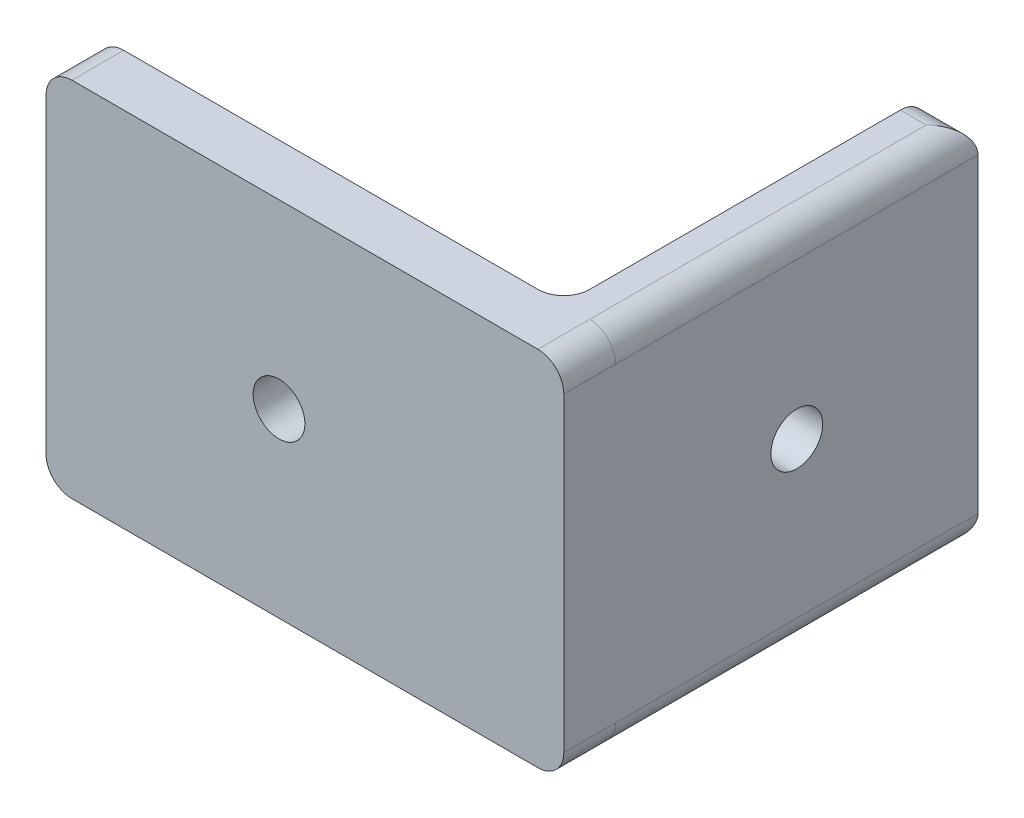
SolidWorks part; units mm, degrees
ref_plane "Front Plane" through (0, 0, 0) normal (0, 0, 1) x (1, 0, 0)
ref_plane "Top Plane" through (0, 0, 0) normal (0, 1, 0) x (1, 0, 0)
ref_plane "Right Plane" through (0, 0, 0) normal (1, 0, 0) x (0, 0, -1)
sketch "Sketch1" plane through (0, 0, 0) normal (0, 0, 1) x (1, 0, 0)
  line L1 (10, 0) -> (190, 0)
  line L2 (0, 10) -> (0, 130)
  line L3 (10, 140) -> (190, 140)
  line L4 (200, 10) -> (200, 130)
  arc A0 (190, 0) -> (200, 10) centre (190, 10) ccw
  arc A1 (190, 140) -> (200, 130) centre (190, 130) cw
  arc A2 (0, 130) -> (10, 140) centre (10, 130) cw
  arc A3 (10, 0) -> (0, 10) centre (10, 10) cw
  point P7 (200, 0)
  point P10 (200, 140)
  point P15 (0, 0)
  dimension "D3" = 10
  dimension "D1" = 200
  dimension "D2" = 140
extrude "Boss-Extrude1" add sketch "Sketch1" against normal blind 20
sketch "Sketch2" plane through (0, 0, -20) normal (0, 0, -1) x (-1, 0, 0)
  line L0 (-190, 140) -> (-10, 140) construction
  line L1 (-180, 140) -> (-200, 140)
  line L2 (-180, 140) -> (-180, 0)
  line L3 (-180, 0) -> (-200, 0)
  line L4 (-200, 140) -> (-200, 0)
  dimension "D1" = 140
  dimension "D2" = 20
extrude "Boss-Extrude2" add sketch "Sketch2" along normal blind 140
fillet "Fillet1" radius 10 5 edges at (190, 0, -160) (190, 140, -160) (180, 70, -20) (200, 0, -90) (200, 140, -90)
sketch "Sketch3" plane through (0, 0, -20) normal (0, 0, -1) x (-1, 0, 0)
  line L0 (-170, 140) -> (-10, 140) construction
  line L1 (-180, 10) -> (-180, 130) construction
  circle A0 centre (-90, 70) radius 10
  point P6 (-104.6444, 74.737)
  dimension "D1" = 20
  dimension "D2" = 70
  dimension "D3" = 90
extrude "Cut-Extrude1" cut sketch "Sketch3" against normal through all
sketch "Sketch4" plane through (180, 0, 0) normal (-1, 0, 0) x (0, 0, 1)
  line L0 (-150, 140) -> (-30, 140) construction
  line L1 (-20, 140) -> (-20, 0) construction
  circle A0 centre (-90, 70) radius 10
  dimension "D1" = 20
  dimension "D2" = 70
  dimension "D3" = 70
extrude "Cut-Extrude2" cut sketch "Sketch4" against normal through all
